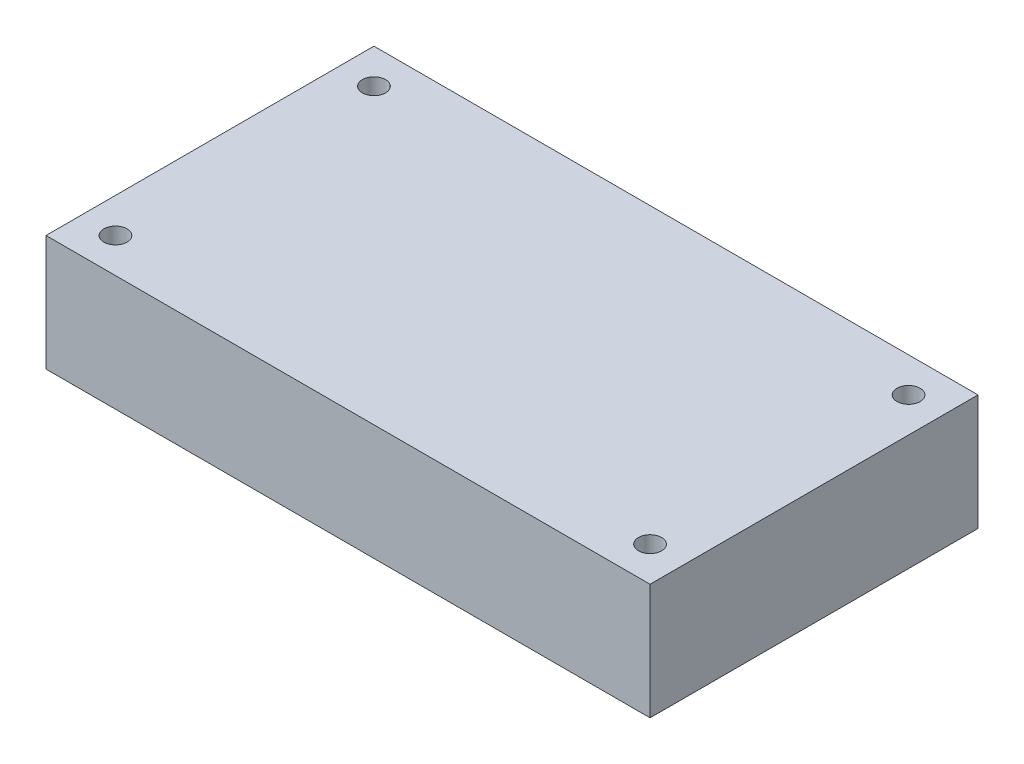
SolidWorks part; units mm, degrees
ref_plane "Front Plane" through (0, 0, 0) normal (0, 0, 1) x (1, 0, 0)
ref_plane "Top Plane" through (0, 0, 0) normal (0, 1, 0) x (1, 0, 0)
ref_plane "Right Plane" through (0, 0, 0) normal (1, 0, 0) x (0, 0, -1)
sketch "Sketch3" plane through (0, 0, 0) normal (0, 1, 0) x (1, 0, 0)
  line L0 (0, 17.9959) -> (0, -17.9959) construction
  line L1 (-33.147, -17.9959) -> (33.147, -17.9959)
  line L2 (-33.147, -17.9959) -> (-33.147, 17.9959)
  line L3 (-33.147, 17.9959) -> (33.147, 17.9959)
  line L4 (33.147, -17.9959) -> (33.147, 17.9959)
  line L5 (-33.147, -17.9959) -> (33.147, 17.9959) construction
  line L6 (-33.147, 17.9959) -> (33.147, -17.9959) construction
  line L7 (-33.147, 0) -> (33.147, 0) construction
  circle A0 centre (-29.337, 14.1859) radius 1.27
  circle A1 centre (29.337, 14.1859) radius 1.27
  circle A2 centre (29.337, -14.1859) radius 1.27
  circle A3 centre (-29.337, -14.1859) radius 1.27
  point P0 (0, 0)
  dimension "D3" = 3.81
  dimension "D1" = 66.294
  dimension "D2" = 35.9918
  dimension "D4" = 3.81
extrude "Boss-Extrude1" add sketch "Sketch3" along normal blind 12.7
